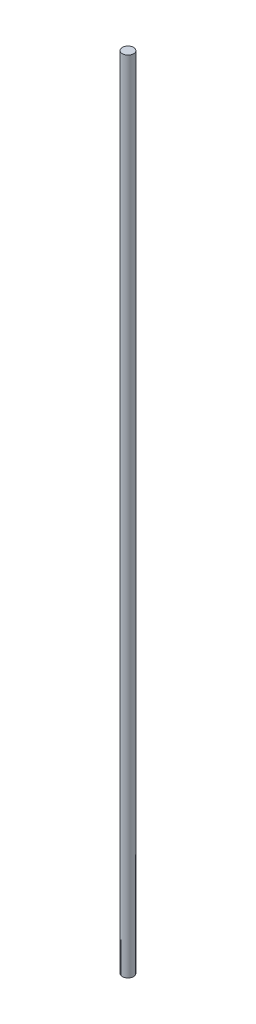
SolidWorks part; units mm, degrees
ref_plane "Plan de face" through (0, 0, 0) normal (0, 0, 1) x (1, 0, 0)
ref_plane "Plan de dessus" through (0, 0, 0) normal (0, 1, 0) x (1, 0, 0)
ref_plane "Plan de droite" through (0, 0, 0) normal (1, 0, 0) x (0, 0, -1)
sketch "Esquisse1" plane through (0, 0, 0) normal (0, 1, 0) x (1, 0, 0)
  circle A0 centre (0, 0) radius 3
  dimension "D1" = 6
extrude "Boss.-Extru.1" add sketch "Esquisse1" along normal blind 430 contours A0
